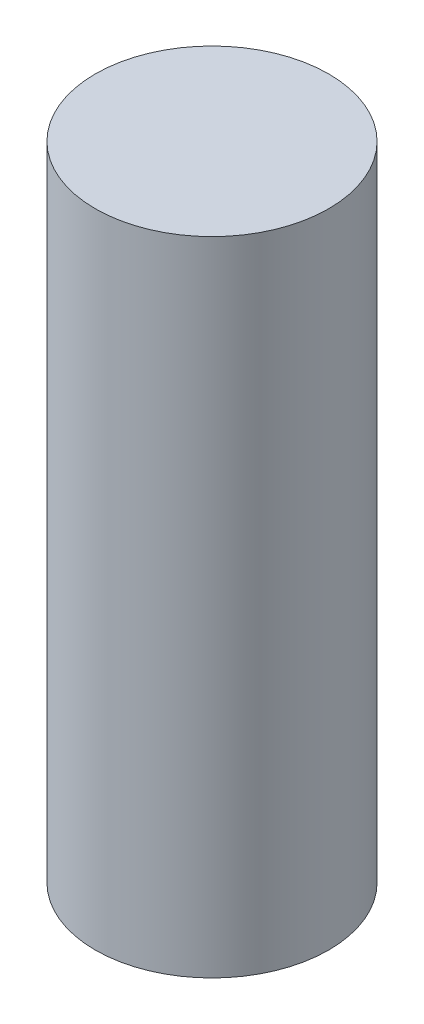
SolidWorks part; units mm, degrees
ref_plane "Front Plane" through (0, 0, 0) normal (0, 0, 1) x (1, 0, 0)
ref_plane "Top Plane" through (0, 0, 0) normal (0, 1, 0) x (1, 0, 0)
ref_plane "Right Plane" through (0, 0, 0) normal (1, 0, 0) x (0, 0, -1)
sketch "Sketch1" plane through (0, 0, 0) normal (0, 1, 0) x (1, 0, 0)
  circle A0 centre (0, 0) radius 2
extrude "Boss-Extrude1" add sketch "Sketch1" along normal blind 11
sketch "Sketch2" plane through (0, 11, 0) normal (0, 1, 0) x (1, 0, 0)
  line L0 (0, 2) -> (0, -2) construction
  circle A0 centre (0, 0) radius 2 construction
sketch "Sketch3" plane through (0, 0, 0) normal (0, -1, 0) x (1, 0, 0)
  line L0 (0, 2) -> (0, -2) construction
